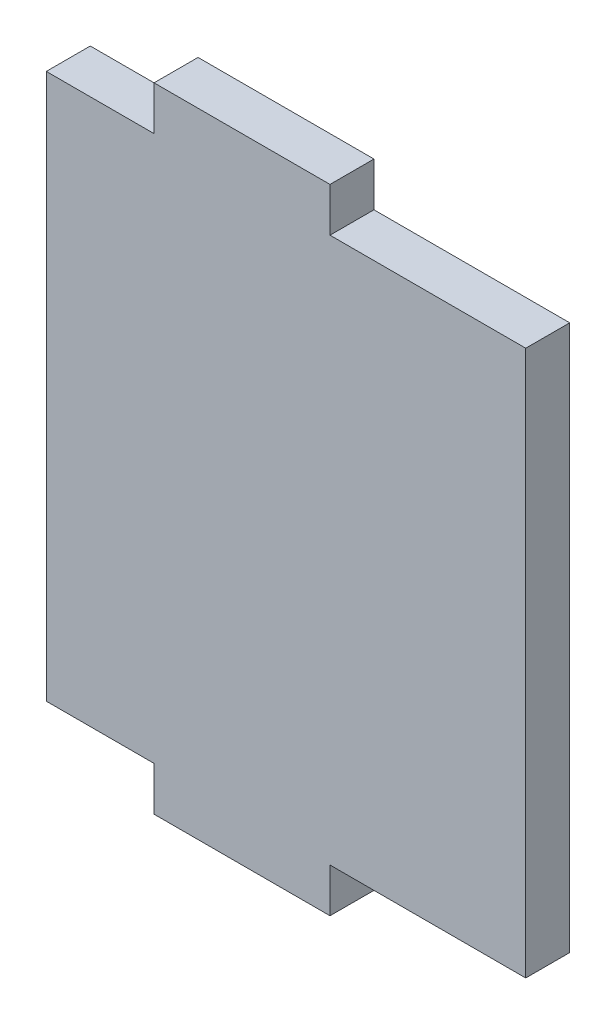
SolidWorks part; units mm, degrees
ref_plane "Front Plane" through (0, 0, 0) normal (0, 0, 1) x (1, 0, 0)
ref_plane "Top Plane" through (0, 0, 0) normal (0, 1, 0) x (1, 0, 0)
ref_plane "Right Plane" through (0, 0, 0) normal (1, 0, 0) x (0, 0, -1)
sketch "Sketch1" plane through (0, 0, 0) normal (0, 0, 1) x (1, 0, 0)
  line L0 (5, 31) -> (5, 36)
  line L1 (-27.25, 31) -> (-15, 31)
  line L2 (-27.25, 31) -> (-27.25, -31)
  line L3 (-27.25, -31) -> (-15, -31)
  line L4 (27.25, 31) -> (27.25, -31)
  line L5 (5, 36) -> (-15, 36)
  line L6 (-15, 36) -> (-15, 31)
  line L7 (5, 31) -> (27.25, 31)
  line L8 (0, 0) -> (33.5636, 0) construction
  line L9 (5, -31) -> (5, -36)
  line L10 (5, -36) -> (-15, -36)
  line L11 (-15, -36) -> (-15, -31)
  line L12 (5, -31) -> (27.25, -31)
  line L13 (-27.25, -31) -> (-15, -31)
  line L14 (-27.25, 31) -> (-15, 31)
  dimension "D1" = 54.5
  dimension "D2" = 62
  dimension "D4" = 27.25
  dimension "D5" = 20
  dimension "D6" = 22.25
  dimension "D7" = 5
extrude "Boss-Extrude1" add sketch "Sketch1" along normal blind 5
